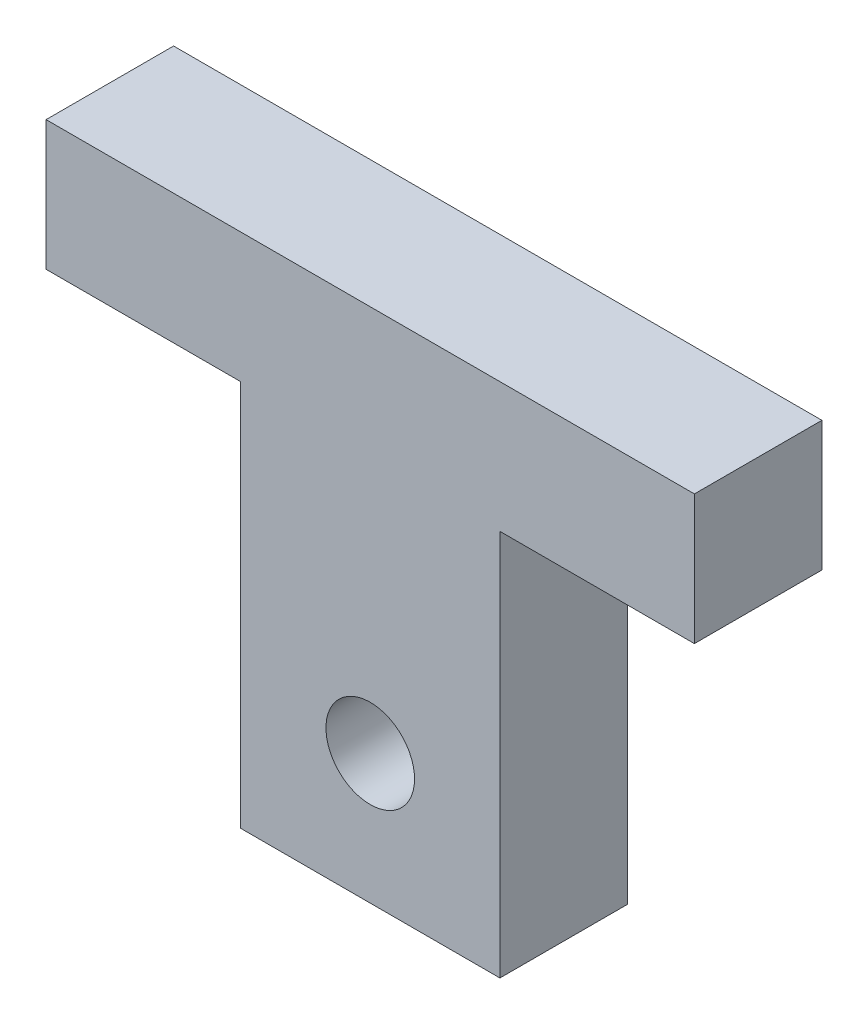
SolidWorks part; units mm, degrees
ref_plane "Front Plane" through (0, 0, 0) normal (0, 0, 1) x (1, 0, 0)
ref_plane "Top Plane" through (0, 0, 0) normal (0, 1, 0) x (1, 0, 0)
ref_plane "Right Plane" through (0, 0, 0) normal (1, 0, 0) x (0, 0, -1)
sketch "Sketch1" plane through (0, 0, 0) normal (0, 0, 1) x (1, 0, 0)
  line L0 (-15, -3) -> (-6, -3)
  line L1 (-15, -3) -> (15, -3) construction
  line L2 (-15, -3) -> (-15, 3)
  line L3 (-15, 3) -> (15, 3)
  line L4 (15, -3) -> (15, 3)
  line L5 (-15, -3) -> (15, 3) construction
  line L6 (-15, 3) -> (15, -3) construction
  line L7 (-6, -3) -> (-6, -20.9)
  line L8 (-6, -20.9) -> (6, -20.9)
  line L9 (6, -20.9) -> (6, -3)
  line L10 (6, -3) -> (15, -3)
  line L11 (0, -20.9) -> (0, 0) construction
  line L12 (0, -14.9) -> (6, -14.9) construction
  line L13 (-6, -8.9) -> (6, -8.9) construction
  line L14 (-2.05, -14.9) -> (-2.05, -20.9) construction
  line L15 (-2.05, -14.9) -> (-2.05, -8.9) construction
  circle A0 centre (0, -14.9) radius 2.05
  point P0 (0, 0)
  point P12 (0, -3)
  dimension "D5" = 4.1
  dimension "D1" = 6
  dimension "D2" = 30
  dimension "D4" = 12
  dimension "D3" = 12
  dimension "D6" = 5.9
extrude "Boss-Extrude1" add sketch "Sketch1" along normal blind 5.9
equation "\"e\" = 5.9"
equation "\"D6@Sketch1\"= \"e\""
equation "\"D1@Boss-Extrude1\"= \"e\""
